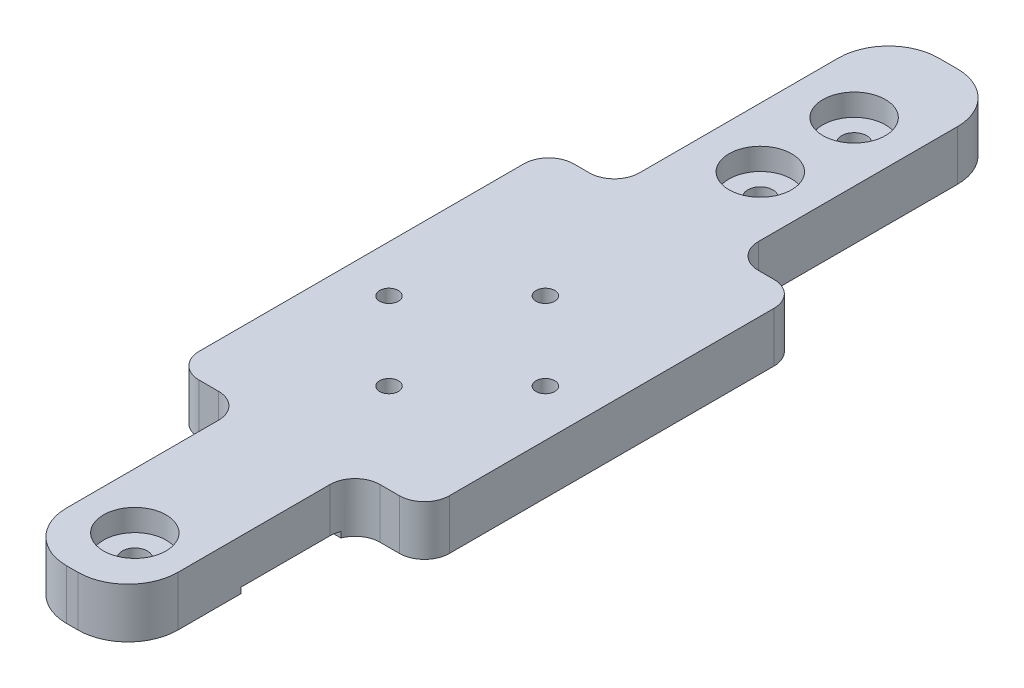
SolidWorks part; units mm, degrees
ref_plane "Front Plane" through (0, 0, 0) normal (0, 0, 1) x (1, 0, 0)
ref_plane "Top Plane" through (0, 0, 0) normal (0, 1, 0) x (1, 0, 0)
ref_plane "Right Plane" through (0, 0, 0) normal (1, 0, 0) x (0, 0, -1)
sketch "Sketch1" plane through (0, 0, 0) normal (0, 1, 0) x (1, 0, 0)
  line L1 (-20, -70) -> (20, -70)
  line L2 (-20, -70) -> (-20, 70)
  line L3 (-20, 70) -> (20, 70)
  line L4 (20, -70) -> (20, 70)
  line L5 (-20, -70) -> (20, 70) construction
  line L6 (-20, 70) -> (20, -70) construction
  point P0 (0, 0)
  dimension "D1" = 40
  dimension "D2" = 140
extrude "Boss-Extrude1" add sketch "Sketch1" along normal blind 8
sketch "Sketch2" plane through (0, 8, 0) normal (0, 1, 0) x (1, 0, 0)
  line L0 (9.5085, 70) -> (-9.5085, 70)
  line L1 (20, 70) -> (-20, 70) construction
  line L2 (8.7579, -36.2391) -> (9.5725, 79.0533) construction
  line L3 (-9.5085, 70) -> (-9.5085, 26.1813)
  line L4 (-30.5, 26.1813) -> (30.5, 26.1813) construction
  line L5 (-9.5085, 26.1813) -> (-20, 26.1813)
  line L6 (-20, 70) -> (-20, -70) construction
  line L7 (9.5085, 70) -> (9.5085, 26.1813)
  line L8 (9.5085, 26.1813) -> (20, 26.1813)
  line L9 (20, -70) -> (20, 70) construction
  line L10 (0, -3.1085) -> (0, 108.3702) construction
  line L11 (20, 26.1813) -> (20, 70)
  line L12 (20, 70) -> (9.5085, 70)
  line L13 (-9.5085, 70) -> (-20, 70)
  line L14 (-20, 70) -> (-20, 26.1813)
  line L15 (8.9051, -70) -> (-8.9051, -70)
  line L16 (-20, -70) -> (20, -70) construction
  line L17 (8.9051, -70) -> (8.9051, -33.7032)
  line L18 (-60.6197, -33.7032) -> (60.6197, -33.7032) construction
  line L19 (8.9051, -33.7032) -> (20, -33.7032)
  line L20 (8.9051, -70) -> (20, -70)
  line L21 (20, -70) -> (20, -33.7032)
  line L22 (-8.9051, -70) -> (-20, -70)
  line L23 (-20, -70) -> (-20, -33.7032)
  line L24 (-20, -33.7032) -> (-8.9051, -33.7032)
  line L25 (-8.9051, -33.7032) -> (-8.9051, -70)
  spline S0 degree 3 poles (8.64, -23.0242) (8.7653, -27.9972) (8.9709, -36.3327) (9.2891, -49.6725) (9.4824, -58.0392) (9.596, -63.0434) knots 0.000241 0.000241 0.000241 0.000241 0.015174 0.025271 0.040296 0.040296 0.040296 0.040296 construction
  point P41 (0, 0)
  line M12 (20, -70) -> (20, 70)
  line M13 (20, 70) -> (-20, 70)
  line M14 (-20, 70) -> (-20, -70)
  line M15 (-20, -70) -> (20, -70)
extrude "Cut-Extrude1" cut sketch "Sketch2" against normal through all both contours L7 L8 M12 M13 | L25 L24 M14 M15 | L19 L17 M15 M12 | L5 L3 M13 M14
fillet "Fillet3" radius 8 4 edges at (9.5085, 4, -70) (-9.5085, 4, -70) (-8.9051, 4, 70) (8.9051, 4, 70)
fillet "Fillet4" radius 4 8 edges at (-8.9051, 4, 33.7032) (-20, 4, 33.7032) (20, 4, 33.7032) (8.9051, 4, 33.7032) (20, 4, -26.1813) (9.5085, 4, -26.1813) (-20, 4, -26.1813) (-9.5085, 4, -26.1813)
sketch "Sketch3" plane through (0, 8, 0) normal (0, 1, 0) x (1, 0, 0)
  circle A0 centre (12.5, -6.8626) radius 1.5
  circle A1 centre (0, 5.6374) radius 1.5
  circle A2 centre (-12.5, -6.8626) radius 1.5
  circle A3 centre (0, -19.3626) radius 1.5
  dimension "D1" = 3
extrude "Cut-Extrude2" cut sketch "Sketch3" against normal through all both
sketch "Sketch4" plane through (8.9051, 0, 0) normal (1, 0, 0) x (0, 0, -1)
  line L0 (-62, 0) -> (-37.7032, 0) construction
  line L1 (-36.2391, 0) -> (-51.9391, 0)
  line L2 (-36.2391, 0) -> (-36.2391, 0.9)
  line L3 (-36.2391, 0.9) -> (-51.9391, 0.9)
  line L4 (-51.9391, 0) -> (-51.9391, 0.9)
  line L5 (-36.2391, 0) -> (-36.2391, -3.8) construction
  line L6 (-51.9391, -3.8) -> (-51.9391, 0) construction
  line L7 (-51.9391, -3.8) -> (-36.2391, -3.8) construction
  point P8 (0, 0)
  dimension "D1" = 4.7
extrude "Cut-Extrude3" cut sketch "Sketch4" along normal through all both and the other way through all
sketch "Sketch5" plane through (0, 0, 0) normal (0, -1, 0) x (1, 0, 0)
  circle A0 centre (12.5, 6.8626) radius 3.05
  circle A1 centre (0, -5.6374) radius 3.05
  circle A2 centre (-12.5, 6.8626) radius 3.05
  circle A3 centre (0, 19.3626) radius 3.05
  point P12 (0, 10.979)
  dimension "D1" = 6.1
extrude "Cut-Extrude4" cut sketch "Sketch5" against normal blind 5.5
sketch "Sketch6" plane through (0, 0, 0) normal (0, -1, 0) x (1, 0, 0)
  line L0 (-0.9051, 70) -> (0.9051, 70) construction
  line L1 (1.5085, -70) -> (-1.5085, -70) construction
  circle A0 centre (0, 60) radius 2
  circle A1 centre (0, -55) radius 2
  circle A2 centre (0, -40) radius 2
  dimension "D1" = 4
  dimension "D2" = 10
  dimension "D3" = 15
  dimension "D4" = 15
extrude "Cut-Extrude5" cut sketch "Sketch6" against normal through all both and the other way through all
sketch "Sketch7" plane through (0, 8, 0) normal (0, 1, 0) x (1, 0, 0)
  circle A0 centre (0, 55) radius 5
  circle A1 centre (0, -60) radius 5
  circle A2 centre (0, 40) radius 5
  dimension "D1" = 10
extrude "Cut-Extrude6" cut sketch "Sketch7" against normal blind 3.5
